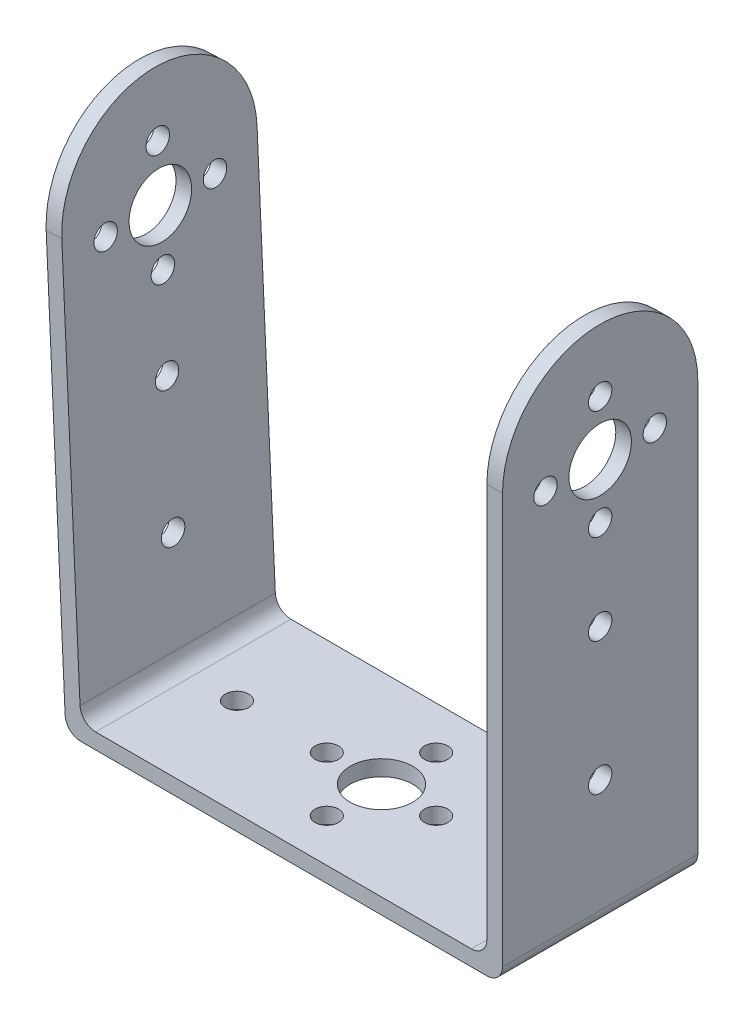
SolidWorks part; units mm, degrees
ref_plane "Front Plane" through (0, 0, 0) normal (0, 0, 1) x (1, 0, 0)
ref_plane "Top Plane" through (0, 0, 0) normal (0, 1, 0) x (1, 0, 0)
ref_plane "Right Plane" through (0, 0, 0) normal (1, 0, 0) x (0, 0, -1)
sketch "Sketch1" plane through (0, 0, 0) normal (0, 0, 1) x (1, 0, 0)
  line L4 (27.9991, 67) -> (25.9991, 67)
  line L17 (-26.0009, 2) -> (-29.0009, 67)
  line L23 (-29.0009, 67) -> (-30.9988, 66.9078)
  line L24 (-30.9988, 66.9078) -> (-27.9107, 0)
  line L25 (-27.9107, 0) -> (-26.0009, 0)
  line L26 (25.9991, 67) -> (25.9991, 2)
  line L27 (25.9991, 2) -> (-26.0009, 2)
  line L28 (27.9991, 67) -> (27.9991, 0)
  line L29 (27.9991, 0) -> (-26.0009, 0)
  point P4 (0, 0)
  dimension "D1" = 2
  dimension "D7" = 2
  dimension "D2" = 55
  dimension "D3" = 2
  dimension "D4" = 65
  dimension "D5" = 52
  dimension "D6" = 2
  dimension "D9" = 90
extrude "Boss-Extrude1" add sketch "Sketch1" against normal blind 25
sketch "Sketch4" plane through (-27.8514, -1.2854, 0) normal (-0.9989, -0.0461, 0) x (0, 0, 1)
  line L0 (-12.5, 1.2868) -> (-12.5, 17.7868) construction
  line L1 (-25, 1.2868) -> (0, 1.2868) construction
  line L2 (-12.5, 17.7868) -> (-12.5, 34.7868) construction
  line L3 (-12.5, 34.7868) -> (-12.5, 53.2868) construction
  line L4 (-25, 68.2658) -> (0, 68.2658) construction
  line L5 (-25, 68.2658) -> (-25, 1.2868) construction
  line L6 (0, 68.2658) -> (0, 1.2868) construction
  line L7 (-25, 55.7658) -> (-25, 68.2658)
  line L8 (-25, 68.2658) -> (0, 68.2658)
  line L9 (0, 68.2658) -> (0, 55.7658)
  circle A0 centre (-12.5, 53.2868) radius 4
  circle A1 centre (-12.5, 53.2868) radius 7 construction
  circle A6 centre (-12.5, 34.7868) radius 1.5
  circle A7 centre (-12.5, 17.7868) radius 1.5
  arc A8 (0, 55.7658) -> (-25, 55.7658) centre (-12.5, 55.7658) ccw
  circle A11 centre (-12.5, 46.2868) radius 1.5
  circle A12 centre (-19.5, 53.2868) radius 1.5
  circle A13 centre (-12.5, 60.2868) radius 1.5
  circle A14 centre (-5.5, 53.2868) radius 1.5
  dimension "D1" = 4
  dimension "D2" = 16.5
  dimension "D5" = 8
  dimension "D6" = 14
  dimension "D3" = 17
  dimension "D4" = 18.5
extrude "Cut-Extrude3" cut sketch "Sketch4" against normal blind 2
sketch "Sketch5" plane through (27.9991, 0, 0) normal (1, 0, 0) x (0, 0, -1)
  line L0 (12.5, 0) -> (12.5, 16.5) construction
  line L1 (25, 0) -> (0, 0) construction
  line L2 (12.5, 16.5) -> (12.5, 33.5) construction
  line L3 (12.5, 33.5) -> (12.5, 52) construction
  line L4 (25, 67) -> (0, 67) construction
  line L5 (0, 0) -> (0, 67) construction
  line L6 (25, 0) -> (25, 67) construction
  line L7 (0, 54.5) -> (0, 67)
  line L8 (0, 67) -> (25, 67)
  line L9 (25, 67) -> (25, 54.5)
  circle A0 centre (12.5, 52) radius 4
  circle A1 centre (12.5, 52) radius 7 construction
  circle A2 centre (5.5, 52) radius 1.5
  circle A3 centre (12.5, 59) radius 1.5
  circle A4 centre (19.5, 52) radius 1.5
  circle A5 centre (12.5, 45) radius 1.5
  circle A6 centre (12.5, 33.5) radius 1.5
  circle A7 centre (12.5, 16.5) radius 1.5
  arc A8 (25, 54.5) -> (0, 54.5) centre (12.5, 54.5) ccw
  line M10 (0, 67) -> (0, 0)
  line M12 (25, 0) -> (25, 67)
  line M13 (25, 67) -> (0, 67)
  dimension "D1" = 4
  dimension "D2" = 18.5
  dimension "D5" = 8
  dimension "D6" = 14
  dimension "D7" = 3
  dimension "D3" = 17
  dimension "D4" = 16.5
extrude "Cut-Extrude4" cut sketch "Sketch5" against normal blind 2 contours A8 L8 M10 | A8 M12 M13 | A3 | A4 | A5 | A2 | A6 | A7 | A0
sketch "Sketch6" plane through (0, 2, 0) normal (0, 1, 0) x (1, 0, 0)
  line L0 (-0.0009, 0) -> (-0.0009, 25) construction
  line L1 (25.9991, 0) -> (-26.0009, 0) construction
  line L2 (25.9991, 25) -> (-26.0009, 25) construction
  line L3 (-0.0009, 12.5) -> (18.4991, 12.5) construction
  line L4 (-0.0009, 12.5) -> (-18.5009, 12.5) construction
  circle A0 centre (-0.0009, 12.5) radius 4
  circle A1 centre (-0.0009, 12.5) radius 7 construction
  circle A2 centre (-7.0009, 12.5) radius 1.5
  circle A3 centre (-0.0009, 19.5) radius 1.5
  circle A4 centre (6.9991, 12.5) radius 1.5
  circle A5 centre (-0.0009, 5.5) radius 1.5
  circle A6 centre (18.4991, 12.5) radius 1.5
  circle A7 centre (-18.5009, 12.5) radius 1.5
  dimension "D1" = 18.5
  dimension "D3" = 14
  dimension "D4" = 3
  dimension "D2" = 18.5
extrude "Cut-Extrude5" cut sketch "Sketch6" against normal blind 2
fillet "Fillet2" radius 2 4 edges at (-27.9107, 0, -12.5) (-26.0009, 2, -12.5) (25.9991, 2, -12.5) (27.9991, 0, -12.5)
